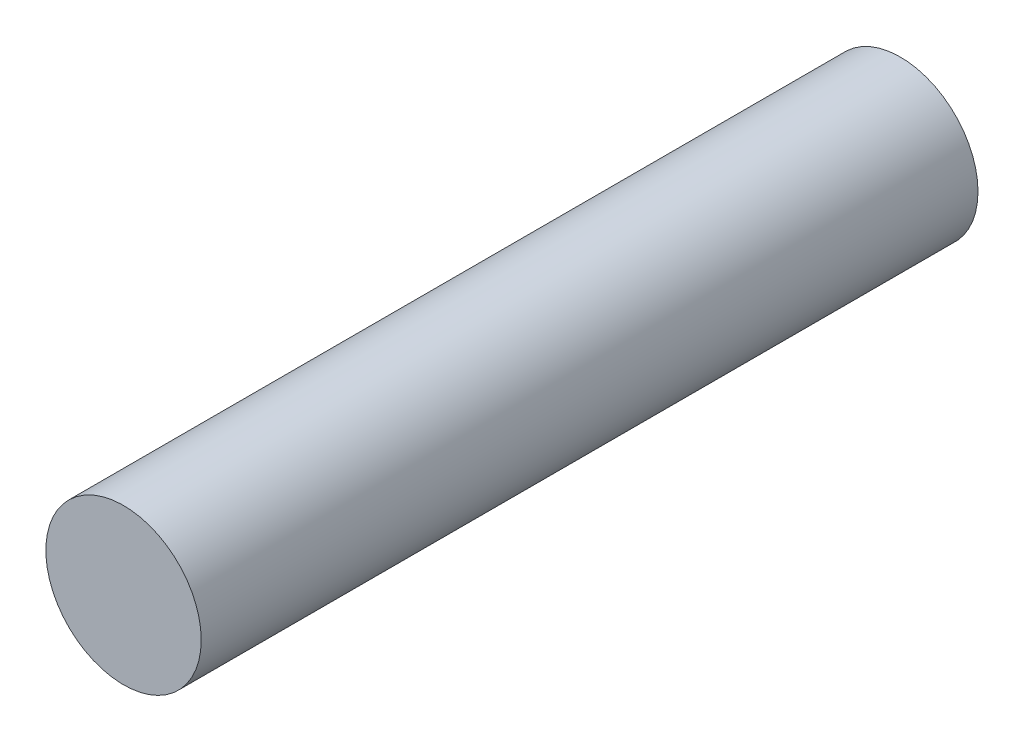
SolidWorks part; units mm, degrees
ref_plane "Plan de face" through (0, 0, 0) normal (0, 0, 1) x (1, 0, 0)
ref_plane "Plan de dessus" through (0, 0, 0) normal (0, 1, 0) x (1, 0, 0)
ref_plane "Plan de droite" through (0, 0, 0) normal (1, 0, 0) x (0, 0, -1)
sketch "Esquisse1" plane through (0, 0, 0) normal (0, 0, 1) x (1, 0, 0)
  circle A0 centre (0, 0) radius 10
  dimension "D1" = 20
extrude "Boss.-Extru.1" add sketch "Esquisse1" along normal blind 100
